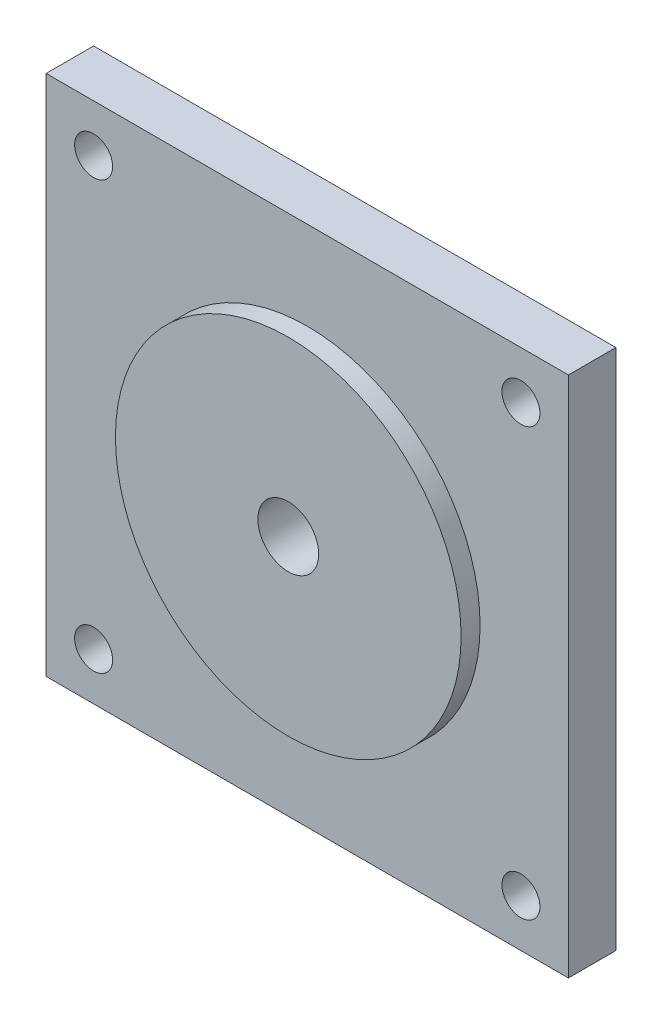
SolidWorks part; units mm, degrees
ref_plane "Front Plane" through (0, 0, 0) normal (0, 0, 1) x (1, 0, 0)
ref_plane "Top Plane" through (0, 0, 0) normal (0, 1, 0) x (1, 0, 0)
ref_plane "Right Plane" through (0, 0, 0) normal (1, 0, 0) x (0, 0, -1)
sketch "Sketch1" plane through (0, 0, 0) normal (0, 0, 1) x (1, 0, 0)
  line L1 (-27.5, 27.5) -> (27.5, 27.5)
  line L2 (-27.5, 27.5) -> (-27.5, -27.5)
  line L3 (-27.5, -27.5) -> (27.5, -27.5)
  line L4 (27.5, 27.5) -> (27.5, -27.5)
  circle A0 centre (0, 0) radius 3.2
  circle A1 centre (-22.5, 22.5) radius 2
  circle A2 centre (22.5, 22.5) radius 2
  circle A3 centre (-22.5, -22.5) radius 2
  circle A4 centre (22.5, -22.5) radius 2
  dimension "D5" = 6.4
  dimension "D6" = 4
  dimension "D7" = 4
  dimension "D8" = 4
  dimension "D9" = 4
  dimension "D1" = 55
  dimension "D2" = 55
  dimension "D3" = 27.5
  dimension "D4" = 27.5
  dimension "D10" = 5
  dimension "D11" = 5
  dimension "D12" = 5
  dimension "D13" = 5
  dimension "D14" = 5
  dimension "D15" = 5
  dimension "D16" = 5
  dimension "D17" = 5
extrude "Boss-Extrude1" add sketch "Sketch1" along normal blind 5
sketch "Sketch2" plane through (0, 0, 5) normal (0, 0, 1) x (1, 0, 0)
  circle A0 centre (0, 0) radius 18.2
  circle A1 centre (0, 0) radius 3.2
  dimension "D1" = 36.4
  dimension "D2" = 6.4
extrude "Boss-Extrude2" add sketch "Sketch2" along normal blind 2
